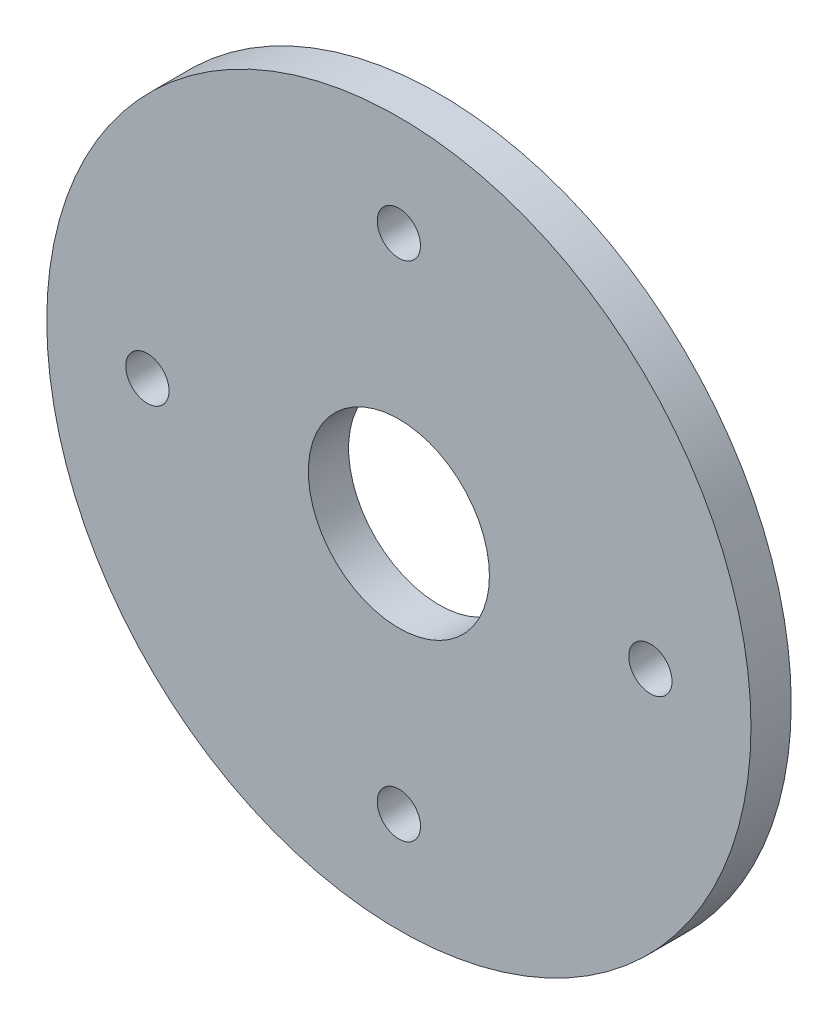
SolidWorks part; units mm, degrees
material "Plain Carbon Steel"
ref_plane "Front" through (0, 0, 0) normal (0, 0, 1) x (1, 0, 0)
ref_plane "Top" through (0, 0, 0) normal (0, 1, 0) x (1, 0, 0)
ref_plane "Right" through (0, 0, 0) normal (1, 0, 0) x (0, 0, -1)
sketch "Sketch1" plane through (0, 0, 0) normal (0, 0, 1) x (1, 0, 0)
  line L1 (0, 0) -> (-70, 0)
  line L2 (0, 0) -> (0, 145)
  line L4 (-70, 0) -> (-70, 145)
  arc A0 (0, 145) -> (-70, 145) centre (-35, 145) ccw
  circle A1 centre (-35, 145) radius 9
  circle A2 centre (-35, 145) radius 35
  dimension "D1" = 18
  dimension "D3" = 35
  dimension "D2" = 145
extrude "Boss-Extrude1" add sketch "Sketch1" along normal blind 4 contours A0 A2 A1
hole_wizard "M4 Clearance Hole1" positions "Sketch3" profile "Sketch2" hole size "M4" standard "ISO" end condition through all
sketch "Sketch3" plane through (0, 0, 4) normal (0, 0, 1) x (1, 0, 0)
  circle A2 centre (-35, 145) radius 9 construction
  circle A3 centre (-35, 145) radius 9 construction
  point P18 (-35, 170)
  point P29 (-10, 145)
  point P30 (-35, 120)
  point P31 (-60, 145)
  dimension "D10" = 4
  dimension "D3" = 25
  dimension "D2" = 25
  dimension "D4" = 25
  dimension "D9" = 25
sketch "Sketch2" plane through (-35, 170, 4) normal (1, 0, 0) x (0, -1, 0)
  line L0 (0, 0) -> (0, 4)
  line L1 (0, 4) -> (2.15, 4)
  line L2 (2.15, 4) -> (2.15, 0)
  line L5 (2.15, 0) -> (0, 0)
  line L11 (0, -6.35) -> (0, 107.95) construction
  dimension "Thru Hole Dia." = 4.3
  dimension "Thru Hole Depth" = 4
sketch "Sketch4" plane through (0, 0, 0) normal (0, 0, 1) x (1, 0, 0)
  circle A0 centre (-35, 145) radius 9.5
  dimension "D1" = 19
